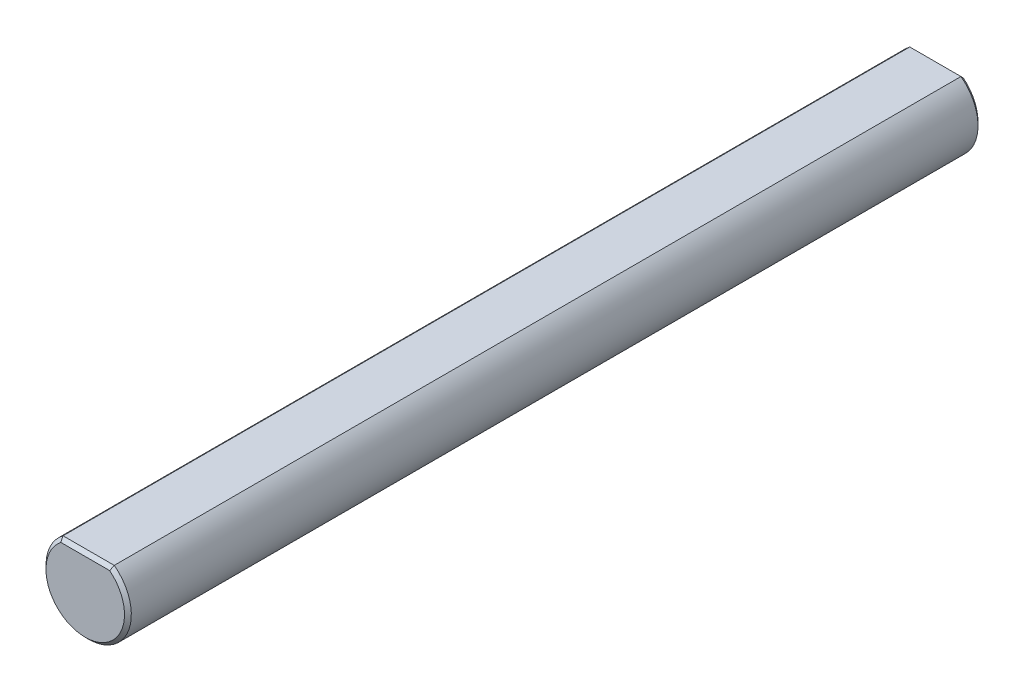
SolidWorks part; units mm, degrees
ref_plane "Front Plane" through (0, 0, 0) normal (0, 0, 1) x (1, 0, 0)
ref_plane "Top Plane" through (0, 0, 0) normal (0, 1, 0) x (1, 0, 0)
ref_plane "Right Plane" through (0, 0, 0) normal (1, 0, 0) x (0, 0, -1)
sketch "Sketch1" plane through (0, 0, 0) normal (0, 0, 1) x (1, 0, 0)
  line L0 (0, -2.5) -> (0, 2) construction
  line L1 (-1.5, 2) -> (1.5, 2)
  circle A0 centre (0, 0) radius 2.5
  dimension "D1" = 5
  dimension "D2" = 4.5
extrude "Boss-Extrude1" add sketch "Sketch1" along normal mid plane 50 contours A0 L0 L1 | L0 A0 L1
chamfer "Chamfer1" distance 0.2 angle 45 4 edges at (0, 2, 25) (0, -2.5, 25) (0, 2, -25) (0, -2.5, -25)
